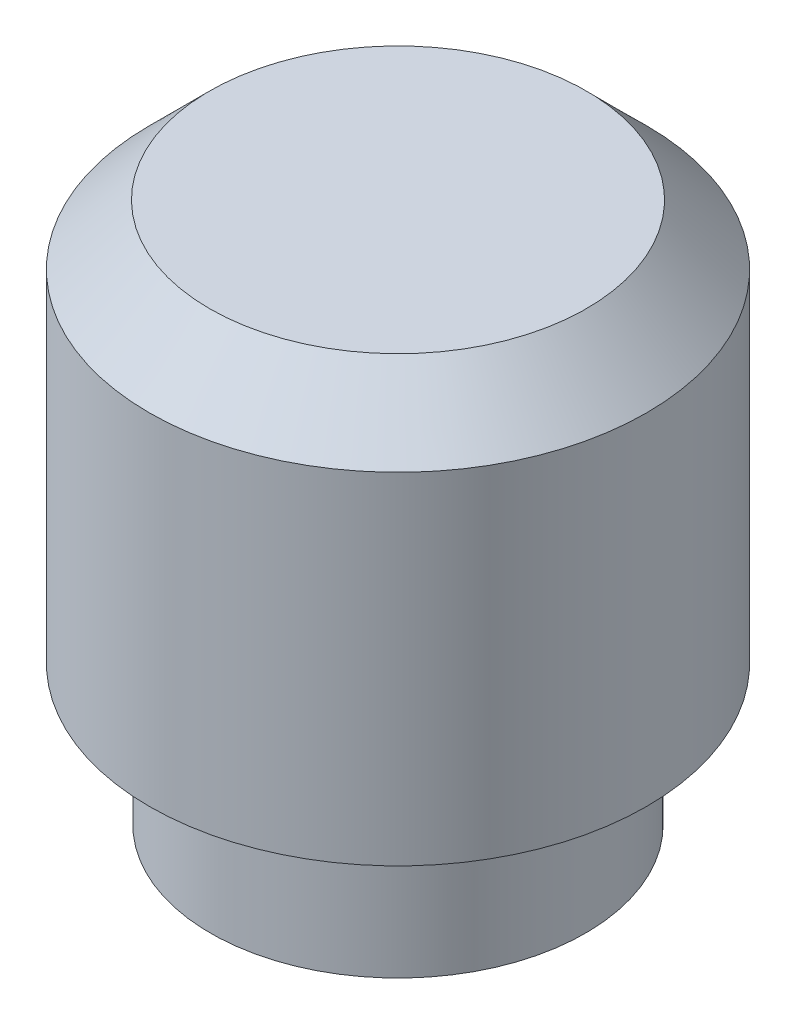
SolidWorks part; units mm, degrees
ref_plane "Front Plane" through (0, 0, 0) normal (0, 0, 1) x (1, 0, 0)
ref_plane "Top Plane" through (0, 0, 0) normal (0, 1, 0) x (1, 0, 0)
ref_plane "Right Plane" through (0, 0, 0) normal (1, 0, 0) x (0, 0, -1)
sketch "Sketch1" plane through (0, 0, 0) normal (0, 0, 1) x (1, 0, 0)
  line L0 (0, 0) -> (0, 80.0374) construction
  line L1 (0, 6.858) -> (3.1496, 6.858)
  line L2 (3.1496, 6.858) -> (3.1496, 1.778)
  line L3 (3.1496, 1.778) -> (2.3749, 1.778)
  line L4 (2.3749, 1.778) -> (2.3749, 0)
  line L5 (2.3749, 0) -> (1.524, 0)
  line L6 (1.524, 0) -> (1.524, 1.778)
  line L7 (1.524, 1.778) -> (0, 2.727)
  line L8 (0, 2.727) -> (0, 6.858)
  dimension "D1" = 6.2992
  dimension "D2" = 3.048
  dimension "D3" = 2.3749
  dimension "D4" = 1.778
  dimension "D5" = 6.858
  dimension "D6" = 58.09
revolve "Revolve1" add sketch "Sketch1" angle 360 about L0
fillet "Fillet1" radius 0.127 1 edges at (0, 1.778, -2.3749)
chamfer "Chamfer1" distance 0.762 angle 45 1 edges at (0, 6.858, -3.1496)
